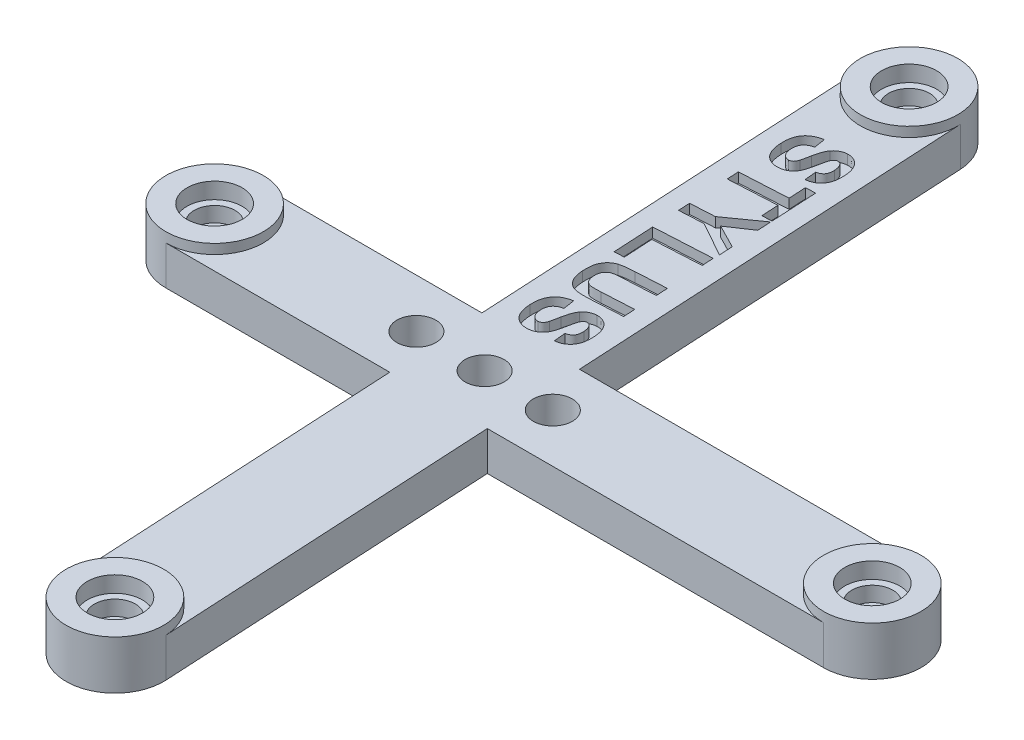
SolidWorks part; units mm, degrees
ref_plane "Front Plane" through (0, 0, 0) normal (0, 0, 1) x (1, 0, 0)
ref_plane "Top Plane" through (0, 0, 0) normal (0, 1, 0) x (1, 0, 0)
ref_plane "Right Plane" through (0, 0, 0) normal (1, 0, 0) x (0, 0, -1)
sketch "Sketch1" plane through (0, 0, 0) normal (0, 1, 0) x (1, 0, 0)
  line L0 (0, 0) -> (-4.6353, 86.1454) construction
  line L1 (-29.8678, 40.102) -> (37.6322, 40.102) construction
  line L2 (-29.8678, 40.102) -> (-2.1578, 40.102) construction
  line L3 (-9.6281, 85.8767) -> (-7.4341, 45.102)
  line L4 (-7.4341, 45.102) -> (-29.8678, 45.102)
  line L5 (-22.5105, 85.1836) -> (13.1044, 87.0999) construction
  line L6 (0.3575, 86.414) -> (2.5804, 45.102)
  line L7 (2.5804, 45.102) -> (37.6322, 45.102)
  line L8 (-11.3209, -0.6092) -> (19.1252, 1.0291) construction
  line L9 (-29.8678, 35.102) -> (-6.896, 35.102)
  line L10 (-6.896, 35.102) -> (-4.9928, -0.2687)
  line L11 (4.9928, 0.2687) -> (3.1185, 35.102)
  line L12 (3.1185, 35.102) -> (37.6322, 35.102)
  arc A0 (-9.6281, 85.8767) -> (0.3575, 86.414) centre (-4.6353, 86.1454) cw
  arc A1 (37.6322, 45.102) -> (37.6322, 35.102) centre (37.6322, 40.102) cw
  arc A2 (4.9928, 0.2687) -> (-4.9928, -0.2687) centre (0, 0) cw
  arc A3 (-29.8678, 35.102) -> (-29.8678, 45.102) centre (-29.8678, 40.102) cw
  dimension "D1" = 67.5
  dimension "D2" = 86.27
  dimension "D3" = 86.92
  dimension "D4" = 27.71
  dimension "D5" = 40.16
  dimension "D6" = 5
  dimension "D7" = 5
  dimension "D8" = 90
  dimension "D9" = 5
  dimension "D10" = 5
  dimension "D11" = 90
  dimension "D12" = 5
  dimension "D13" = 5
  dimension "D14" = 5
  dimension "D15" = 5
extrude "Boss-Extrude1" add sketch "Sketch1" along normal blind 4
sketch "Sketch2" plane through (0, 4, 0) normal (0, 1, 0) x (1, 0, 0)
  circle A0 centre (-4.6353, 86.1454) radius 5
  circle A1 centre (-29.8678, 40.102) radius 5
  circle A2 centre (37.6322, 40.102) radius 5
  circle A3 centre (0, 0) radius 5
extrude "Boss-Extrude2" add sketch "Sketch2" along normal blind 1
sketch "Sketch3" plane through (0, 5, 0) normal (0, 1, 0) x (1, 0, 0)
  circle A0 centre (-29.8678, 40.102) radius 1.5
  circle A1 centre (-4.6353, 86.1454) radius 1.5
  circle A2 centre (37.6322, 40.102) radius 1.5
  circle A3 centre (0, 0) radius 1.5
  dimension "D1" = 3
  dimension "D2" = 3
  dimension "D3" = 3
  dimension "D4" = 3
extrude "Cut-Extrude1" cut sketch "Sketch3" against normal through all
sketch "Sketch4" plane through (0, 5, 0) normal (0, 1, 0) x (1, 0, 0)
  circle A0 centre (-4.6353, 86.1454) radius 2.1
  circle A1 centre (-29.8678, 40.102) radius 2.1
  circle A2 centre (37.6322, 40.102) radius 2.1
  circle A3 centre (0, 0) radius 2.1
  dimension "D1" = 4.2
  dimension "D2" = 4.2
  dimension "D3" = 4.2
  dimension "D4" = 4.2
extrude "Cut-Extrude2" cut sketch "Sketch4" against normal blind 3.2
sketch "Sketch5" plane through (0, 5, 0) normal (0, 1, 0) x (1, 0, 0)
  circle A0 centre (-4.6353, 86.1454) radius 2.825
  circle A1 centre (-29.8678, 40.102) radius 2.825
  circle A2 centre (37.6322, 40.102) radius 2.825
  circle A3 centre (0, 0) radius 2.825
  dimension "D1" = 5.65
  dimension "D2" = 5.65
  dimension "D3" = 5.65
  dimension "D4" = 5.65
extrude "Cut-Extrude3" cut sketch "Sketch5" against normal blind 1.65
sketch "Sketch6" plane through (0, 4, 0) normal (0, 1, 0) x (1, 0, 0)
  line L0 (-29.8678, 40.102) -> (37.6322, 40.102) construction
  line L1 (-4.6353, 86.1454) -> (0, 0) construction
  circle A0 centre (-2.1578, 40.102) radius 2
  circle A1 centre (4.8422, 40.102) radius 2
  circle A2 centre (-9.1578, 40.102) radius 2
  dimension "D1" = 4
  dimension "D2" = 4
  dimension "D3" = 4
  dimension "D4" = 7
  dimension "D5" = 7
extrude "Cut-Extrude4" cut sketch "Sketch6" against normal through all
sketch "Sketch7" plane through (0, 4, 0) normal (0, 1, 0) x (1, 0, 0)
  line L0 (-29.8678, 40.102) -> (37.6322, 40.102) construction
  line L1 (-4.6353, 86.1454) -> (0, 0) construction
  line L2 (-7.216, 78.272) -> (-5.5964, 48.1732) construction
  text T0 "STYLUS" font "Arial" height 6
  dimension "D1" = 3
extrude "Cut-Extrude5" cut sketch "Sketch7" against normal blind 1
